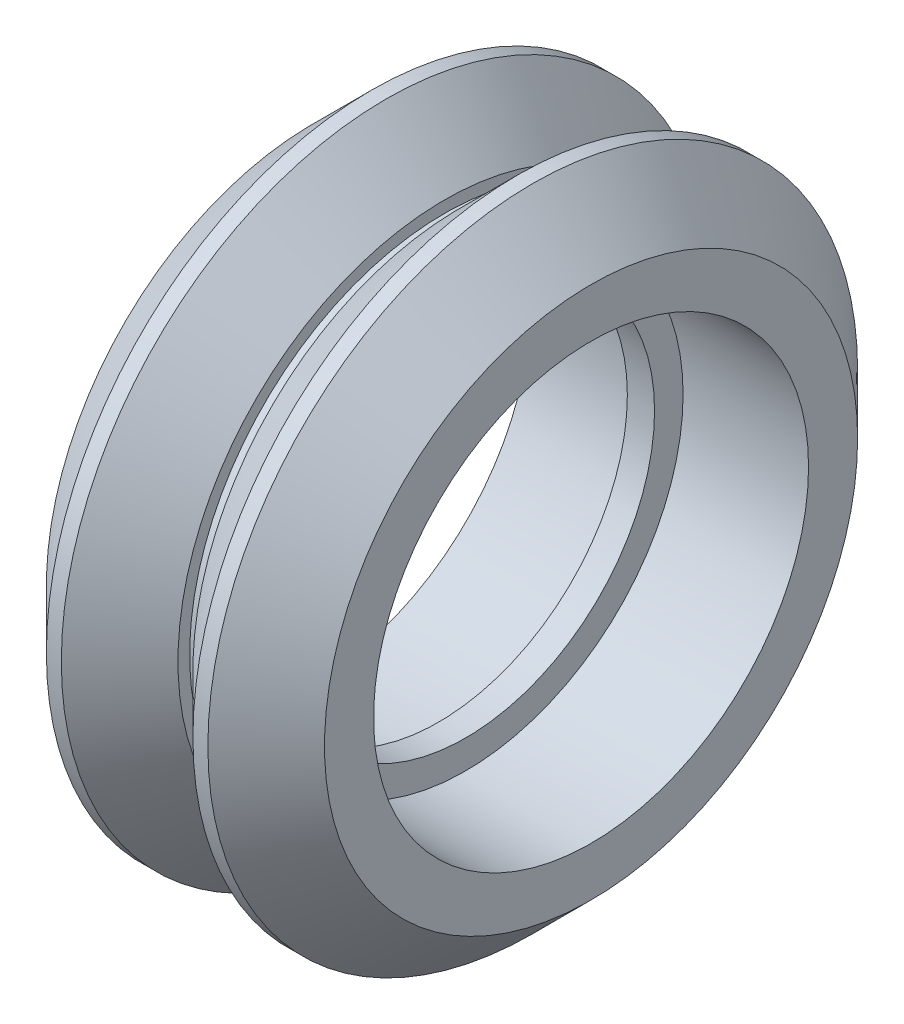
SolidWorks part; units mm, degrees
material "Delrin 2700 NC010, Low Viscosity Acetal Copolymer (SS)"
ref_plane "Front Plane" through (0, 0, 0) normal (0, 0, 1) x (1, 0, 0)
ref_plane "Top Plane" through (0, 0, 0) normal (0, 1, 0) x (1, 0, 0)
ref_plane "Right Plane" through (0, 0, 0) normal (1, 0, 0) x (0, 0, -1)
sketch "Sketch1" plane through (0, 0, 0) normal (0, 0, 1) x (1, 0, 0)
  line L0 (0.5, 6.95) -> (-0.5, 6.95)
  line L1 (-0.5, 6.95) -> (-0.5, 8)
  line L2 (-0.5, 8) -> (-5.115, 8)
  line L3 (-5.115, 8) -> (-5.115, 9.805)
  line L4 (-5.115, 9.805) -> (-2.97, 11.95)
  line L5 (-2.97, 11.95) -> (-2.42, 11.95)
  line L6 (0, 12) -> (0, 6.95) construction
  line L7 (5.115, 9.805) -> (2.97, 11.95)
  line L8 (5.115, 8) -> (5.115, 9.805)
  line L9 (0.5, 8) -> (5.115, 8)
  line L10 (0.5, 6.95) -> (0.5, 8)
  line L11 (0, 0) -> (-12.6359, 0) construction
  line L12 (-2.42, 11.95) -> (-0.275, 9.805)
  line L13 (-0.275, 9.805) -> (-0.275, 9.375)
  line L14 (-0.275, 9.375) -> (0.275, 9.375)
  line L15 (0.275, 9.805) -> (0.275, 9.375)
  line L16 (2.97, 11.95) -> (2.42, 11.95)
  line L17 (2.42, 11.95) -> (0.275, 9.805)
  line L18 (0, -990.625) -> (0, 49009.375) construction
  point P20 (0, 9.375)
  point P23 (0.4035, -4.5591)
  point P25 (0, 0)
  dimension "D1" = 0.55
  dimension "D2" = 16
  dimension "D3" = 23.9
  dimension "D4" = 1
  dimension "D5" = 45
  dimension "D6" = 10.23
  dimension "D7" = 18.75
  dimension "D8" = 13.9
  dimension "D9" = 0.55
revolve "Revolve1" add sketch "Sketch1" angle 360 about L11
